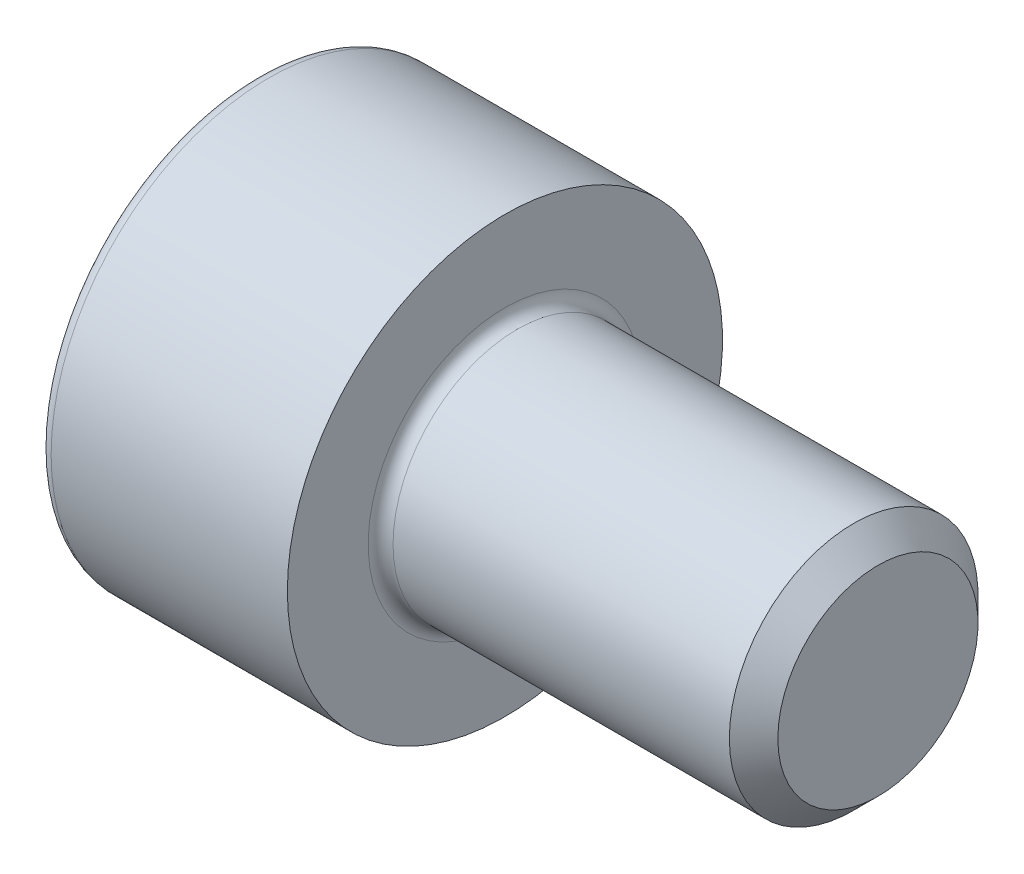
SolidWorks part; units mm, degrees
ref_plane "Plane1" through (0, 0, 0) normal (0, 0, 1) x (1, 0, 0)
ref_plane "Plane2" through (0, 0, 0) normal (0, 1, 0) x (1, 0, 0)
ref_plane "Plane3" through (0, 0, 0) normal (1, 0, 0) x (0, 0, -1)
sketch "BodySke" plane through (0, 0, 0) normal (0, 0, 1) x (1, 0, 0)
  line L0 (0, 0) -> (0, 3.5)
  line L1 (0, 3.5) -> (4, 3.5)
  line L2 (4, 3.5) -> (4, 2)
  line L3 (4, 2) -> (9.61, 2)
  line L4 (10, 1.61) -> (10, 0)
  line L5 (10, 0) -> (0, 0)
  line L6 (-31.75, 0) -> (127, 0) construction
  line L8 (10, 1.61) -> (9.61, 2)
  line L10 (10, -1.61) -> (9.61, -2) construction
  line L11 (3.3, 9.525) -> (3.3, 3.175) construction
  line L12 (4, 9.525) -> (4, 3.175) construction
  line L13 (-35, 9.525) -> (-35, 3.175) construction
  dimension "Diameter" = 4
  dimension "Head_ht" = 4
  dimension "Length" = 6
  dimension "Body_ch_ang" = 45
  dimension "Head_dia" = 7
  dimension "Minor_dia" = 3.22
  dimension "Advance" = 0.7
  dimension "Thread_nom" = 6
  dimension "Thread_length" = 45
revolve "Base-Revolve" add sketch "BodySke" angle 360 about L6
cosmetic thread "ThreadCosmetic" parameters "Thread_length"=3.9, "Thread_minor"=3.22
fillet "Fillet1" radius 0.2 1 edges at (4, 0, 2)
fillet "Fillet2" radius 0.2 1 edges at (0, 0, 3.5)
sketch "Sketch2" plane through (0, 0, 0) normal (0, 0, 1) x (1, 0, 0)
  line L0 (0, 1.5355) -> (2, 1.5355)
  line L1 (2, 1.5355) -> (2.8865, 0)
  line L2 (-31.75, 0) -> (127, 0) construction
  line L3 (2.8865, 0) -> (0, 0)
  line L4 (0, 0) -> (0, 1.5355)
  line L6 (0, 0) -> (47.625, 0) construction
  dimension "D1" = 1.5355
  dimension "D2" = 60
  dimension "Depth" = 2
revolve "Hex-PreBroach" cut sketch "Sketch2" angle 360 about L6
sketch "Sketch3" plane through (0, 0, 0) normal (-1, 0, 0) x (0, 0.5, 0.866)
  line L0 (0.8865, 1.5355) -> (-0.8865, 1.5355)
  line L1 (-0.8865, 1.5355) -> (-1.773, 0)
  line L2 (0.8865, 1.5355) -> (1.773, 0)
  line L3 (0.8865, -1.5355) -> (1.773, 0)
  line L4 (0.8865, -1.5355) -> (-0.8865, -1.5355)
  line L5 (-0.8865, -1.5355) -> (-1.773, 0)
  dimension "D1" = 1.5355
  dimension "D2" = 1.5355
  dimension "Hex_size" = 3.071
extrude "Hex" cut sketch "Sketch3" against normal blind 2
sketch "ThdSchSke" plane through (0, 0, 0) normal (0, 0, 1) x (1, 0, 0)
  line L0 (6.1, -1.61) -> (5.8269, -2)
  line L1 (6.1, -1.61) -> (6.3731, -2)
  line L2 (6.3731, -2) -> (6.3731, -2.5)
  line L3 (-3.175, 0) -> (5.1513, 0) construction
  line L4 (0, 3.3) -> (0, -3.3) construction
  line L5 (6.3731, -2.5) -> (5.8269, -2.5)
  line L6 (5.8269, -2.5) -> (5.8269, -2)
  dimension "Thread_minor" = 3.22
  dimension "Diameter" = 4
  dimension "Start" = 6.1
  dimension "SideAngle" = 55
  dimension "VeeAngle" = 70
  dimension "Overcut" = 5
revolve "ThreadSchematic" [suppressed] cut sketch "ThdSchSke" angle 360 about L3
pattern_linear "ThdSchPat" [suppressed]
equation "\"D2@Sketch3\" = \"Hex_size@Sketch3\" / 2"
equation "\"D1@Sketch3\" = \"Hex_size@Sketch3\" / 2"
equation "\"D1@Sketch2\" = \"Hex_size@Sketch3\" / 2"
equation "\"Thread_minor@ThreadCosmetic\"  =  \"Minor_dia@BodySke\""
equation "\"Depth@Sketch2\" =  \"Key_eng@Hex\""
equation "\"Thread_length@ThreadCosmetic\" = ((sgn( (\"Length@BodySke\" - \"Advance@BodySke\" * 3.0) - \"Thread_nom@BodySke\" )-1)*( (\"Length@BodySke\" - \"Advance@BodySke\" * 3.0) - \"Thread_nom@BodySke\" ))/-2+ \"Thread_nom@BodySke\""
equation "\"Thread_minor@ThdSchSke\" = \"Minor_dia@BodySke\""
equation "\"Diameter@ThdSchSke\" = \"Diameter@BodySke\""
equation "\"Overcut@ThdSchSke\" = \"Diameter@BodySke\" * 1.25"
equation "\"Start@ThdSchSke\" = \"Head_ht@BodySke\" + \"Length@BodySke\" - \"Thread_length@ThreadCosmetic\"  '---Non-countersunk---"
equation "\"Num_threads@ThdSchPat\" = int( \"Thread_length@ThreadCosmetic\" / \"Advance@BodySke\" + 0.999 )  + 1"
equation "\"Advance@ThdSchPat\" = \"Thread_length@ThreadCosmetic\" /  (\"Num_threads@ThdSchPat\" - 1) 'relax it"
equation "\"Num_threads@ThdSchPat\" = \"Num_threads@ThdSchPat\" - sgn( \"Num_threads@ThdSchPat\" - 1) '---chamfered tips only---"
